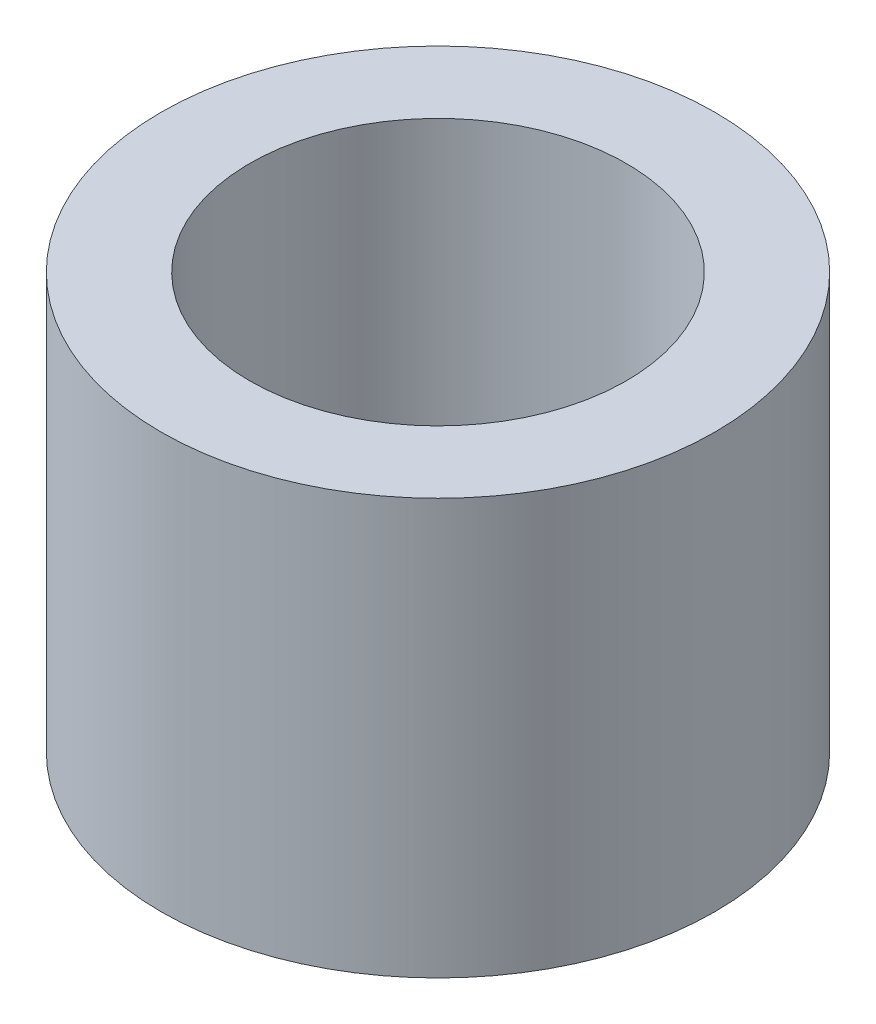
SolidWorks part; units mm, degrees
material "Nylon 6/10"
ref_plane "Front Plane" through (0, 0, 0) normal (0, 0, 1) x (1, 0, 0)
ref_plane "Top Plane" through (0, 0, 0) normal (0, 1, 0) x (1, 0, 0)
ref_plane "Right Plane" through (0, 0, 0) normal (1, 0, 0) x (0, 0, -1)
sketch "Sketch1" plane through (0, 0, 0) normal (0, 1, 0) x (1, 0, 0)
  circle A0 centre (0, 0) radius 2.159
  circle A1 centre (0, 0) radius 3.175
  dimension "D1" = 4.318
  dimension "D2" = 6.35
extrude "Boss-Extrude1" add sketch "Sketch1" along normal blind 4.7625
